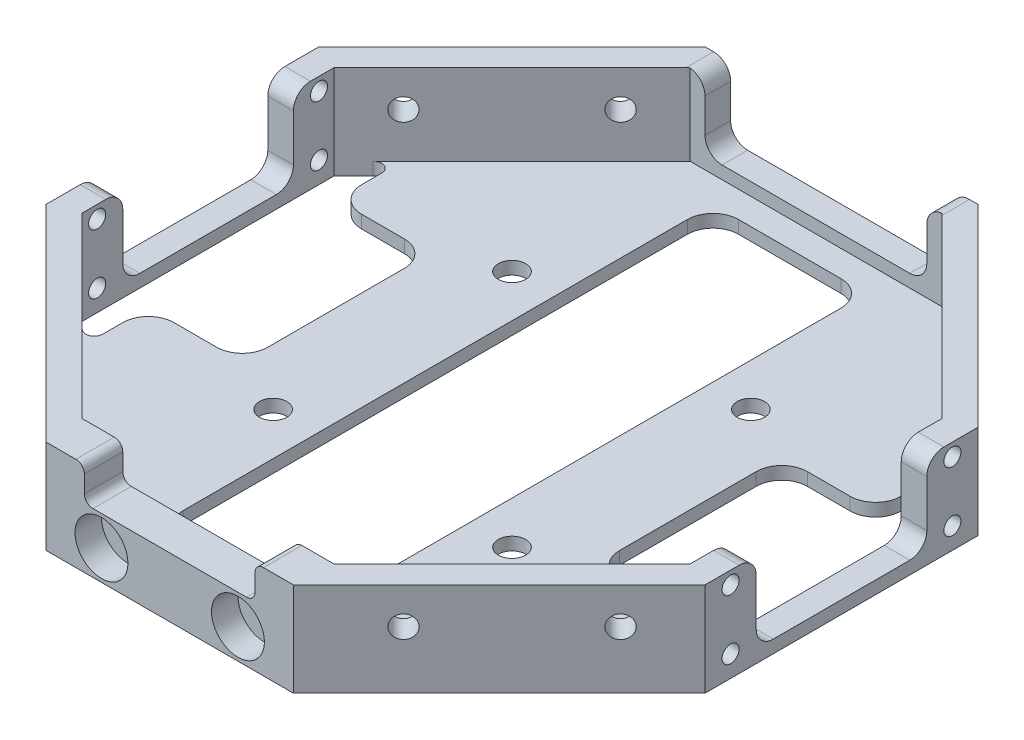
SolidWorks part; units mm, degrees
ref_plane "Front Plane" through (0, 0, 0) normal (0, 0, 1) x (1, 0, 0)
ref_plane "Top Plane" through (0, 0, 0) normal (0, 1, 0) x (1, 0, 0)
ref_plane "Right Plane" through (0, 0, 0) normal (1, 0, 0) x (0, 0, -1)
sketch "Sketch1" plane through (0, 0, 0) normal (0, 1, 0) x (1, 0, 0)
  line L1 (38.6274, 16) -> (16, 38.6274)
  line L2 (16, 38.6274) -> (-16, 38.6274)
  line L3 (-16, 38.6274) -> (-38.6274, 16)
  line L4 (-38.6274, 16) -> (-38.6274, -16)
  line L5 (-38.6274, -16) -> (-16, -38.6274)
  line L6 (-16, -38.6274) -> (16, -38.6274)
  line L7 (16, -38.6274) -> (38.6274, -16)
  line L8 (38.6274, -16) -> (38.6274, 16)
  circle A0 centre (0, 0) radius 38.6274 construction
  dimension "D1" = 32
extrude "Boss-Extrude1" add sketch "Sketch1" along normal blind 11
shell "Shell1" thickness 3
sketch "Sketch2" plane through (27.3137, 0, 27.3137) normal (0.7071, 0, 0.7071) x (0.7071, 0, -0.7071)
  line L0 (0, 11) -> (0, 6.75)
  line L1 (-16, 11) -> (16, 11) construction
  line L2 (0, 6.75) -> (9, 6.75)
  line L3 (0, 6.75) -> (-9, 6.75)
  circle A0 centre (9, 6.75) radius 1.3
  circle A1 centre (-9, 6.75) radius 1.3
extrude "Cut-Extrude1" cut sketch "Sketch2" against normal blind 152
sketch "Sketch3" plane through (-27.3137, 0, 27.3137) normal (-0.7071, 0, 0.7071) x (0.7071, 0, 0.7071)
  line L0 (0, 11) -> (0, 6.75)
  line L1 (-16, 11) -> (16, 11) construction
  line L2 (0, 6.75) -> (9, 6.75)
  line L3 (0, 6.75) -> (-9, 6.75)
  circle A0 centre (9, 6.75) radius 1.3
  circle A1 centre (-9, 6.75) radius 1.3
extrude "Cut-Extrude2" cut sketch "Sketch3" against normal blind 152
sketch "Sketch4" plane through (38.6274, 0, 0) normal (1, 0, 0) x (0, 0, -1)
  line L1 (-16, 11) -> (16, 11) construction
  line L2 (0, 1.5) -> (10, 1.5)
  line L3 (10, 1.5) -> (10, 11)
  line L4 (10, 11) -> (0, 11)
  line L5 (0, 1.5) -> (-10, 1.5)
  line L6 (-10, 1.5) -> (-10, 11)
  line L7 (-10, 11) -> (0, 11)
extrude "Cut-Extrude3" cut sketch "Sketch4" against normal blind 152
sketch "Sketch5" plane through (0, 0, -38.6274) normal (0, 0, -1) x (-1, 0, 0)
  line L0 (0, 11) -> (0, 3)
  line L1 (-16, 11) -> (16, 11) construction
  line L2 (0, 3) -> (13, 3)
  line L3 (13, 3) -> (13, 11)
  line L4 (0, 3) -> (-13, 3)
  line L5 (-13, 3) -> (-13, 11)
  line L6 (-13, 11) -> (13, 11)
  line M3 (16, 11) -> (-16, 11)
extrude "Cut-Extrude4" cut sketch "Sketch5" against normal blind 45 contours L5 L4 L0 M3 | L2 L3 L0 M3
fillet "Fillet1" radius 2 12 edges at (-13, 11, -37.1274) (-13, 3, -37.1274) (13, 11, -37.1274) (13, 3, -37.1274) (37.1274, 11, 10) (37.1274, 1.5, 10) (37.1274, 11, -10) (37.1274, 1.5, -10) (-37.1274, 11, -10) (-37.1274, 1.5, -10) (-37.1274, 11, 10) (-37.1274, 1.5, 10)
sketch "Sketch7" plane through (0, 1.5, 0) normal (0, 1, 0) x (1, 0, 0)
  line L0 (35.6274, -8) -> (35.6274, -10)
  line L1 (35.6274, -8) -> (35.6274, -10) construction
  line L2 (35.6274, -10) -> (31.6274, -10)
  line L3 (31.6274, -10) -> (31.6274, -18.7574)
  line L4 (14.7574, -35.6274) -> (35.6274, -14.7574) construction
  line L5 (31.6274, -18.7574) -> (35.6274, -14.7574)
  line L6 (35.6274, -14.7574) -> (35.6274, -10)
  line L7 (38.6274, 0) -> (-38.6274, 0)
  line L8 (38.6274, -8) -> (38.6274, 8) construction
  line L9 (-38.6274, -8) -> (-38.6274, 8) construction
  line L10 (0, 0) -> (0, 8.7153)
  line L11 (35.6274, 14.7574) -> (35.6274, 10)
  line L12 (31.6274, 18.7574) -> (35.6274, 14.7574)
  line L13 (31.6274, 10) -> (31.6274, 18.7574)
  line L14 (35.6274, 10) -> (31.6274, 10)
  line L15 (-35.6274, 10) -> (-31.6274, 10)
  line L16 (-31.6274, 10) -> (-31.6274, 18.7574)
  line L17 (-31.6274, 18.7574) -> (-35.6274, 14.7574)
  line L18 (-35.6274, 14.7574) -> (-35.6274, 10)
  line L19 (-35.6274, -14.7574) -> (-35.6274, -10)
  line L20 (-31.6274, -18.7574) -> (-35.6274, -14.7574)
  line L21 (-31.6274, -10) -> (-31.6274, -18.7574)
  line L22 (-35.6274, -10) -> (-31.6274, -10)
  line L23 (-35.6274, -8) -> (-35.6274, -10)
extrude "Cut-Extrude6" cut sketch "Sketch7" against normal blind 92
sketch "Sketch6" plane through (38.6274, 0, 0) normal (1, 0, 0) x (0, 0, -1)
  line L0 (-16, 11) -> (-13, 11)
  line L1 (-16, 11) -> (-12, 11) construction
  line L2 (-13, 11) -> (-13, 9.5)
  line L3 (-13, 9.5) -> (-13, 2.5)
  line L4 (0, 0) -> (0, 5.587)
  line L5 (13, 9.5) -> (13, 2.5)
  line L6 (13, 11) -> (13, 9.5)
  line L7 (16, 11) -> (13, 11)
  circle A0 centre (-13, 9.5) radius 1
  circle A1 centre (-13, 2.5) radius 1
  circle A2 centre (13, 2.5) radius 1
  circle A3 centre (13, 9.5) radius 1
  dimension "D1" = 1.5
  dimension "D2" = 7
extrude "Cut-Extrude7" cut sketch "Sketch6" against normal blind 5
sketch "Sketch12" plane through (-35.6274, 0, 0) normal (1, 0, 0) x (0, 0, -1)
  circle A0 centre (-13, 9.5) radius 1
  circle A1 centre (-13, 2.5) radius 1
  circle A2 centre (13, 2.5) radius 1
  circle A3 centre (13, 9.5) radius 1
extrude "Cut-Extrude8" cut sketch "Sketch12" against normal blind 5
fillet "Fillet2" radius 1 12 edges at (-31.6274, 0.75, 10) (-31.6274, 0.75, 18.7574) (-35.6274, 0.75, 10) (35.6274, 0.75, -10) (31.6274, 0.75, -10) (31.6274, 0.75, -18.7574) (31.6274, 0.75, 10) (35.6274, 0.75, 10) (31.6274, 0.75, 18.7574) (-31.6274, 0.75, -10) (-35.6274, 0.75, -10) (-31.6274, 0.75, -18.7574)
sketch "Sketch13" plane through (0, 11, 0) normal (0, 1, 0) x (1, 0, 0)
  line L0 (-16, -38.6274) -> (16, -38.6274)
  line L1 (16, -38.6274) -> (14.5, -40.1274)
  line L2 (0, -38.6274) -> (0, -40.1274)
  line L3 (-14.5, -40.1274) -> (14.5, -40.1274)
  line L4 (-16, -38.6274) -> (-14.5, -40.1274)
  line M12 (-16, -38.6274) -> (16, -38.6274)
extrude "Boss-Extrude2" add sketch "Sketch13" against normal blind 11 contours L4 L3 L2 M12 | L2 L3 L1 L0
sketch "Sketch14" plane through (0, 0, 40.1274) normal (0, 0, 1) x (1, 0, 0)
  line L0 (0, 0) -> (0, 3.5)
  line L1 (-14.5, 0) -> (14.5, 0) construction
  line L2 (0, 3.5) -> (8, 3.5)
  circle A0 centre (8, 3.5) radius 3.1
  circle A1 centre (-8, 3.5) radius 3.1
extrude "Cut-Extrude9" cut sketch "Sketch14" against normal blind 3.1
sketch "Sketch18" plane through (0, 0, 40.1274) normal (0, 0, 1) x (1, 0, 0)
  line L0 (-4.9, 3.5) -> (4.9, 3.5)
  line L1 (0, 3.5) -> (0, 7)
  line L2 (0, 7) -> (10, 7)
  line L3 (10, 7) -> (10, 11)
  line L4 (-14.5, 11) -> (14.5, 11) construction
  line L5 (0, 7) -> (-10, 7)
  line L6 (-10, 7) -> (-10, 11)
  line L7 (-10, 11) -> (10, 11)
  circle A0 centre (-8, 3.5) radius 3.1 construction
  circle A1 centre (-8, 3.5) radius 3.1 construction
  circle A2 centre (8, 3.5) radius 3.1 construction
  line M1 (14.5, 11) -> (-14.5, 11)
extrude "Cut-Extrude10" cut sketch "Sketch18" against normal blind 9.1 contours L6 L5 L2 L3 M1
fillet "Fillet3" radius 1 4 edges at (-10, 7, 37.8774) (-10, 11, 37.8774) (10, 11, 37.8774) (10, 7, 37.8774)
sketch "Sketch19" plane through (0, 0, 0) normal (0, -1, 0) x (-1, 0, 0)
  line L1 (9, 32.5563) -> (-9, 32.5563)
  line L2 (9, 32.5563) -> (9, -32.5563)
  line L3 (9, -32.5563) -> (-9, -32.5563)
  line L4 (-9, 32.5563) -> (-9, -32.5563)
  line L5 (9, 32.5563) -> (-9, -32.5563) construction
  line L6 (9, -32.5563) -> (-9, 32.5563) construction
  line L14 (-32.6274, -11) -> (-23.6274, -11)
  line L16 (-14, -14) -> (0, -14)
  line L34 (-20.6274, 8) -> (-20.6274, -8)
  line L35 (-35.6274, 8) -> (-35.6274, -8)
  line L36 (-32.6274, 11) -> (-23.6274, 11)
  line L37 (32.6274, 11) -> (23.6274, 11)
  line L38 (35.6274, 8) -> (35.6274, -8)
  line L39 (20.6274, 8) -> (20.6274, -8)
  line L40 (32.6274, -11) -> (23.6274, -11)
  line L41 (38.6274, -8) -> (38.6274, 8) construction
  line L42 (11, 38.6274) -> (-11, 38.6274) construction
  line L43 (0, -14) -> (0, 0)
  line L44 (-38.6274, -8) -> (-38.6274, 8) construction
  line L45 (32.6274, 11) -> (35.6274, 11)
  line L46 (32.6274, -11) -> (35.6274, -11)
  line L47 (35.6274, -11) -> (35.6274, 11)
  line L48 (-32.6274, 11) -> (-35.6274, 11)
  line L51 (-32.6274, -11) -> (-35.6274, -11)
  line L52 (-35.6274, -12) -> (-35.6274, -10) construction
  line L53 (-35.6274, -11) -> (-35.6274, 11)
  circle A0 centre (14, -14) radius 1.6
  circle A1 centre (-14, -14) radius 1.6
  circle A2 centre (-14, 14) radius 1.6
  circle A3 centre (14, 14) radius 1.6
  arc A14 (-23.6274, -11) -> (-20.6274, -8) centre (-23.6274, -8) ccw
  arc A15 (-20.6274, 8) -> (-23.6274, 11) centre (-23.6274, 8) ccw
  arc A16 (20.6274, 8) -> (23.6274, 11) centre (23.6274, 8) cw
  arc A17 (23.6274, -11) -> (20.6274, -8) centre (23.6274, -8) cw
  point P12 (0, 0)
  dimension "D2" = 3
  dimension "D3" = 27.6274
  dimension "D4" = 3
extrude "Cut-Extrude12" cut sketch "Sketch19" against normal blind 10
fillet "Fillet4" radius 3 8 edges at (-31.6274, 0.75, -11) (-31.6274, 0.75, 11) (31.6274, 0.75, -11) (31.6274, 0.75, 11) (-9, 0.75, -32.5563) (9, 0.75, -32.5563) (9, 0.75, 32.5563) (-9, 0.75, 32.5563)
